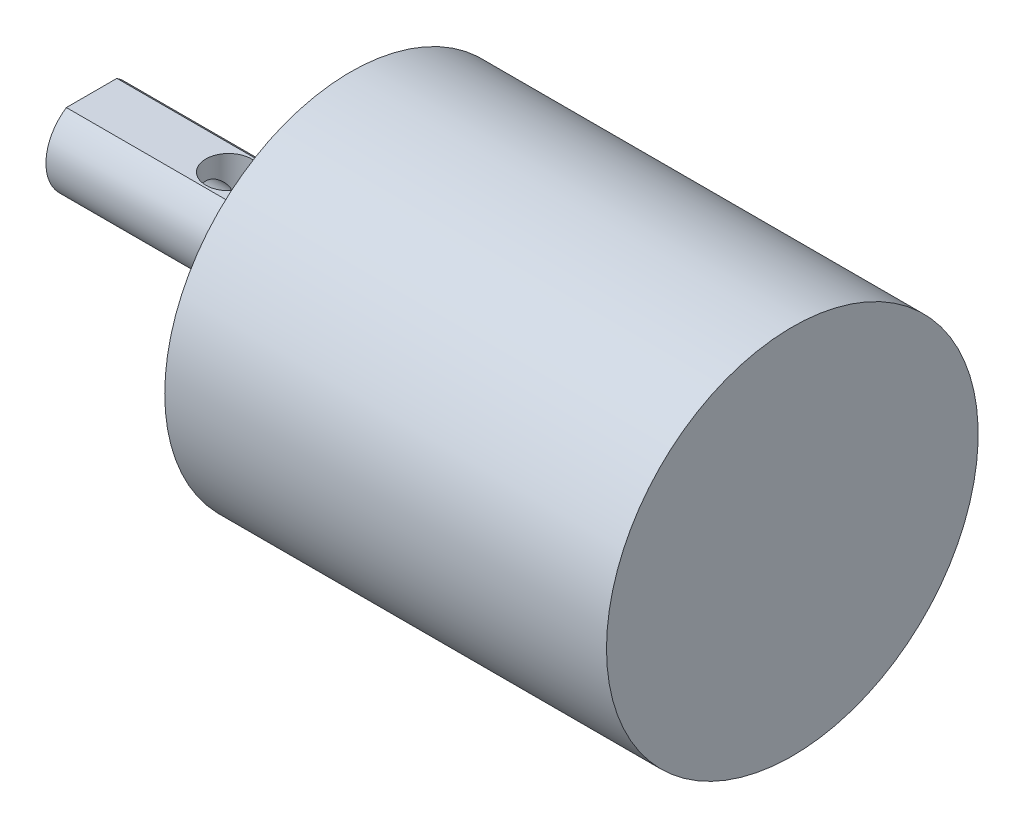
SolidWorks part; units mm, degrees
ref_plane "前视基准面" through (0, 0, 0) normal (0, 0, 1) x (1, 0, 0)
ref_plane "上视基准面" through (0, 0, 0) normal (0, 1, 0) x (1, 0, 0)
ref_plane "右视基准面" through (0, 0, 0) normal (1, 0, 0) x (0, 0, -1)
sketch "草图1" plane through (0, 0, 0) normal (0, 1, 0) x (1, 0, 0)
  line L0 (0, 0) -> (-29, 0)
  line L1 (-29, 0) -> (-29, 5.7)
  line L2 (-29, 5.7) -> (-31.6, 5.7)
  line L3 (-31.6, 5.7) -> (-31.6, 9.2)
  line L4 (-31.6, 9.2) -> (-46, 9.2)
  line L5 (-46, 9.2) -> (-46, 12.2)
  line L6 (-46, 12.2) -> (0, 12.2)
  line L7 (0, 12.2) -> (0, 0)
  dimension "D1" = 29
  dimension "D2" = 5.7
  dimension "D3" = 2.6
  dimension "D4" = 3.5
  dimension "D5" = 14.4
  dimension "D6" = 3
revolve "旋转1" add sketch "草图1" angle 360 about L6
sketch "草图2" plane through (-46, 0, 0) normal (-1, 0, 0) x (0, 0, 1)
  point P0 (-12.2, 0)
sketch "草图9" plane through (-46, 0, 0) normal (-1, 0, 0) x (0, 0, 1)
  line L0 (-12.2, 2.5) -> (-10.5417, 2.5)
  line L1 (-12.2, 2.5) -> (-13.8583, 2.5)
  line L2 (-13.8583, 2.5) -> (-12.2, 2.5)
  circle A0 centre (-12.2, 0) radius 3 construction
  arc A1 (-10.5417, 2.5) -> (-13.8583, 2.5) centre (-12.2, 0) ccw
  dimension "D1" = 1.6583
extrude "切除-拉伸3" cut sketch "草图9" against normal blind 11.5 contours L1 A1 L0
hole_wizard "M3 螺纹孔1" positions "草图10" profile "草图11" tap size "M3" standard "GB"
sketch "草图10" plane through (-46, 0, 0) normal (-1, 0, 0) x (0, 0, 1)
  point P0 (-12.2, 0)
sketch "草图11" plane through (-46, 0, -12.2) normal (0, 1, 0) x (0, 0, 1)
  line L0 (0, 0) -> (0, 8.7511)
  line L1 (0, 8.7511) -> (1.25, 8)
  line L2 (1.25, 8) -> (1.25, 0)
  line L5 (1.25, 0) -> (0, 0)
  line L10 (0, 8.7511) -> (-1.25, 8) construction
  line L11 (0, -6.35) -> (0, 107.95) construction
  dimension "螺纹孔钻头直径" = 2.5
  dimension "螺纹孔钻头深度" = 8
  dimension "导头角度" = 118
cosmetic thread "孔螺蚊线2" parameters "D1"=5.5, "D2"=3
sketch "草图12" plane through (0, 2.5, 0) normal (0, 1, 0) x (1, 0, 0)
  line L0 (-46, 10.5417) -> (-46, 13.8583) construction
  line L1 (-34.5, 10.5417) -> (-46, 10.5417) construction
  circle A0 centre (-37, 12.2) radius 1.5
  point P0 (-37, 12.2)
  dimension "D1" = 3
  dimension "D2" = 9
  dimension "D3" = 1.6583
extrude "切除-拉伸4" cut sketch "草图12" against normal blind 11.5 contours A0
sketch "草图13" plane through (-29, 0, 0) normal (-1, 0, 0) x (0, 0, 1)
  circle A1 centre (-12.2, 9.5) radius 1.5
  circle A2 centre (-3.9728, -4.75) radius 1.5
  circle A3 centre (-20.4272, -4.75) radius 1.5
  point P11 (-12.2, 0)
  dimension "D2" = 3
  dimension "D3" = 3
hole_wizard "M3 螺纹孔2" positions "草图14" profile "草图15" tap size "M3" standard "GB"
sketch "草图14" plane through (-29, 0, 0) normal (-1, 0, 0) x (0, 0, 1)
  point P2 (-12.2, 9.5)
  point P5 (-20.4272, -4.75)
  point P8 (-3.9728, -4.75)
sketch "草图15" plane through (-29, 9.5, -12.2) normal (0, 1, 0) x (0, 0, 1)
  line L0 (0, 0) -> (0, 4.7511)
  line L1 (0, 4.7511) -> (1.25, 4)
  line L2 (1.25, 4) -> (1.25, 0)
  line L5 (1.25, 0) -> (0, 0)
  line L10 (0, 4.7511) -> (-1.25, 4) construction
  line L11 (0, -6.35) -> (0, 107.95) construction
  dimension "螺纹孔钻头直径" = 2.5
  dimension "螺纹孔钻头深度" = 4
  dimension "导头角度" = 118
cosmetic thread "孔螺蚊线3" parameters "D1"=4, "D2"=3
cosmetic thread "孔螺蚊线4" parameters "D1"=4, "D2"=3
cosmetic thread "孔螺蚊线5" parameters "D1"=4, "D2"=3
sketch "草图16" plane through (-31.6, 0, 0) normal (-1, 0, 0) x (0, 0, 1)
  line L0 (-9.6019, -1.5) -> (-12.2, -6)
  line L1 (-18.0095, -1.5) -> (-14.6921, 1.6702)
  arc A0 (-12.2, -6) -> (-18.0095, -1.5) centre (-12.2, 0) ccw
  arc A1 (-13.8583, 2.5) -> (-10.5417, 2.5) centre (-12.2, 0) ccw construction
  arc A2 (-14.6921, 1.6702) -> (-9.6019, -1.5) centre (-12.2, 0) cw
  circle A3 centre (-12.2, 0) radius 6.5 construction
  dimension "D1" = 12
  dimension "D2" = 2.4921
extrude "凸台-拉伸1" add sketch "草图16" along normal blind 0.5 contours A0 L1 A2 L0
sketch "草图4" plane through (-46, 0, 0) normal (-1, 0, 0) x (0, 0, 1)
  circle A0 centre (-12.2, 0) radius 1.5
  point P0 (-12.2, 0)
  dimension "D1" = 3
sketch "草图17" plane through (0, 0, 0) normal (0, 1, 0) x (1, 0, 0)
  line L0 (-46, 12.2) -> (-37, 12.2)
  point P4 (-38.5111, 12.2)
